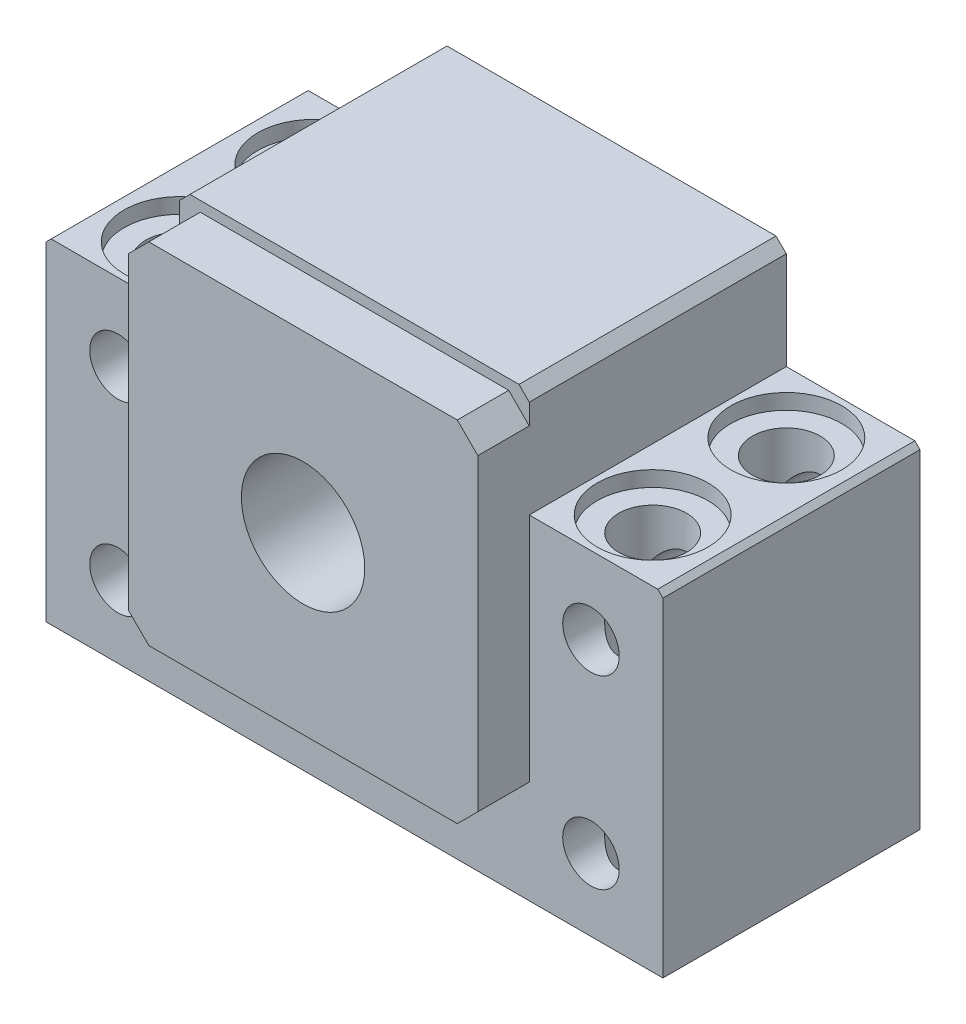
SolidWorks part; units mm, degrees
material "6061 Alloy"
ref_plane "Спереди" through (0, 0, 0) normal (0, 0, 1) x (1, 0, 0)
ref_plane "Сверху" through (0, 0, 0) normal (0, 1, 0) x (1, 0, 0)
ref_plane "Справа" through (0, 0, 0) normal (1, 0, 0) x (0, 0, -1)
sketch "Эскиз1" plane through (0, 0, 0) normal (0, 0, 1) x (1, 0, 0)
  line L0 (0, -25) -> (0, 14) construction
  line L1 (-30, 7) -> (-30, -25)
  line L2 (-30, -25) -> (30, -25)
  line L3 (30, -25) -> (30, 7)
  line L4 (29.5, 7.5) -> (17, 7.5)
  line L5 (17, 7.5) -> (17, 17)
  line L6 (-17, 7.5) -> (-17, 17)
  line L7 (-29.5, 7.5) -> (-30, 7)
  line L8 (-29.5, 7.5) -> (-17, 7.5)
  line L9 (-23, -2.75) -> (-23, 2.75) construction
  line L10 (-16, 18) -> (16, 18)
  line L11 (23, -15.25) -> (23, -20.75) construction
  line L12 (-20.25, -18) -> (-25.75, -18) construction
  line L13 (20.25, -18) -> (25.75, -18) construction
  line L14 (-23, -15.25) -> (-23, -20.75) construction
  line L15 (23, -2.75) -> (23, 2.75) construction
  line L16 (30, 7) -> (29.5, 7.5)
  line L17 (-30, 0) -> (30, 0) construction
  line L18 (-17, 17) -> (-16, 18)
  line L19 (17, 17) -> (16, 18)
  circle A0 centre (0, 0) radius 6
  circle A1 centre (-23, 0) radius 2.75
  circle A2 centre (-23, -18) radius 2.75
  circle A3 centre (23, -18) radius 2.75
  circle A4 centre (23, 0) radius 2.75
  point P6 (30, 7.5)
  point P8 (17, 18)
  point P13 (-17, 18)
  point P16 (-30, 7.5)
  dimension "D1" = 60
  dimension "D9" = 5.5
  dimension "D2" = 46
  dimension "D3" = 30
  dimension "D4" = 25
  dimension "D5" = 32.5
  dimension "D6" = 43
  dimension "D7" = 34
  dimension "D8" = 18
extrude "Бобышка-Вытянуть1" add sketch "Эскиз1" against normal blind 25
sketch "Эскиз2" plane through (0, 0, 0) normal (0, 0, 1) x (1, 0, 0)
  line L0 (-17, 15) -> (-15, 17)
  line L1 (-15, 17) -> (15, 17)
  line L4 (17, 15) -> (17, -15)
  line L5 (15, -17) -> (-15, -17)
  line L6 (-17, -15) -> (-17, 15)
  line L7 (15, 17) -> (17, 15)
  line L8 (-15, -17) -> (-17, -15)
  line L9 (17, -15) -> (15, -17)
  circle A0 centre (0, 0) radius 6
  point P4 (-17, 17)
  point P6 (17, 17)
  point P11 (-17, -17)
  point P12 (17, -17)
extrude "Бобышка-Вытянуть2" add sketch "Эскиз2" along normal blind 5
sketch "Эскиз3" plane through (0, 0, 0) normal (0, 1, 0) x (1, 0, 0)
  line L0 (23, 25) -> (23, 0) construction
  line L1 (0, 25) -> (0, -5) construction
  line L2 (-17, 25) -> (-29.5, 25) construction
  line L3 (30, 25) -> (30, 0) construction
  line L4 (-30, 19) -> (30, 19) construction
  line L8 (-30, 6) -> (30, 6) construction
  line L10 (-23, 25) -> (-23, 0) construction
  circle A0 centre (-23, 19) radius 3.3
  circle A1 centre (-23, 6) radius 3.3
  circle A2 centre (23, 6) radius 3.3
  circle A3 centre (23, 19) radius 3.3
  dimension "D1" = 6
  dimension "D2" = 13
  dimension "D3" = 46
  dimension "D4" = 7
extrude "Вырез-Вытянуть1" cut sketch "Эскиз3" against normal through all from offset 7.5
sketch "Эскиз4" plane through (0, 0, 0) normal (0, 1, 0) x (1, 0, 0)
  circle A0 centre (-23, 19) radius 5.4
  circle A1 centre (-23, 6) radius 5.4
  circle A2 centre (23, 6) radius 5.4
  circle A3 centre (23, 19) radius 5.4
extrude "Вырез-Вытянуть2" cut sketch "Эскиз4" against normal blind 1.5 from offset 7.5
